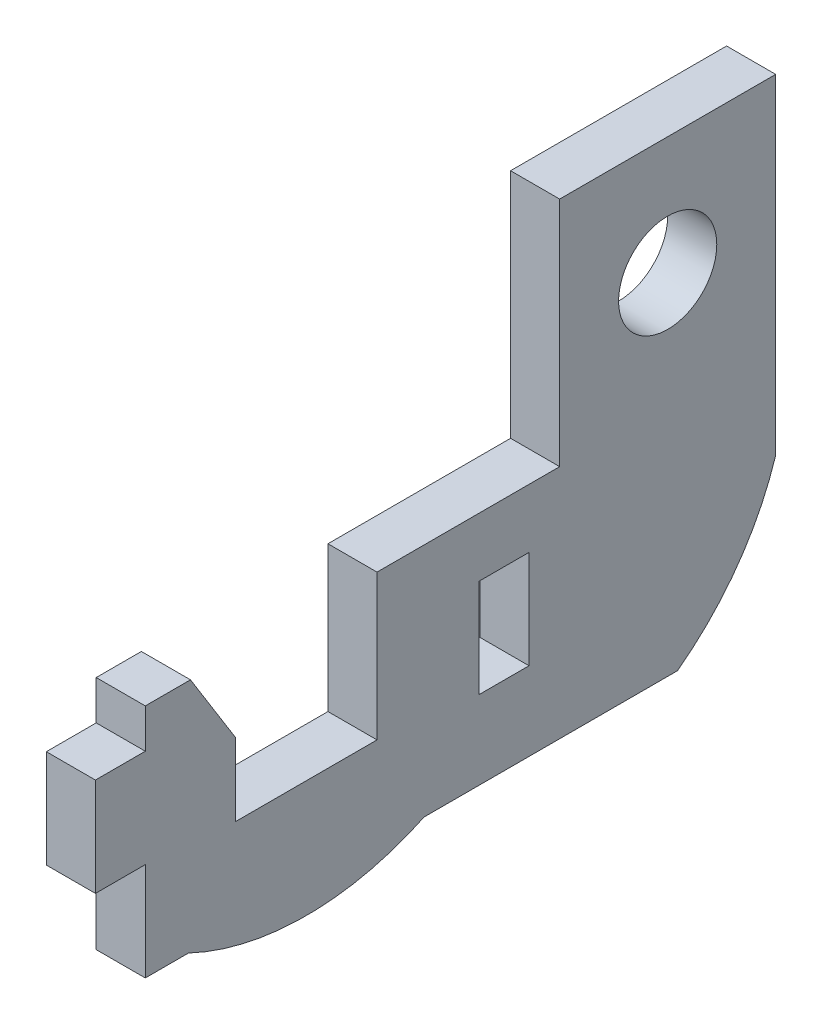
SolidWorks part; units mm, degrees
ref_plane "Front Plane" through (0, 0, 0) normal (0, 0, 1) x (1, 0, 0)
ref_plane "Top Plane" through (0, 0, 0) normal (0, 1, 0) x (1, 0, 0)
ref_plane "Right Plane" through (0, 0, 0) normal (1, 0, 0) x (0, 0, -1)
sketch "Sketch1" plane through (0, 0, 0) normal (1, 0, 0) x (0, 0, -1)
  line L0 (-6.985, 7.62) -> (6.985, 7.62)
  line L1 (-6.985, 7.62) -> (-6.985, -7.366)
  line L2 (-6.985, -7.366) -> (-18.796, -7.366)
  line L3 (-33.782, -7.366) -> (-33.782, -9.906)
  line L4 (-33.782, -9.906) -> (-37.0078, -9.906)
  line L5 (-37.0078, -9.906) -> (-37.0078, -16.256)
  line L6 (-37.0078, -16.256) -> (-33.782, -16.256)
  line L7 (-33.782, -16.256) -> (-33.782, -22.606)
  line L8 (-33.782, -22.606) -> (6.985, -22.606)
  line L9 (6.985, -22.606) -> (6.985, 7.62)
  line L10 (-37.0078, -13.081) -> (6.985, -13.081) construction
  line L11 (-18.796, -7.366) -> (-18.796, -16.764)
  line L13 (-8.9662, -11.176) -> (-12.192, -11.176)
  line L14 (-8.9662, -11.176) -> (-8.9662, -17.526)
  line L15 (-8.9662, -17.526) -> (-12.192, -17.526)
  line L16 (-12.192, -11.176) -> (-12.192, -17.526)
  line L17 (-8.9662, -11.176) -> (-12.192, -17.526) construction
  line L18 (-18.796, -16.764) -> (-27.94, -16.764)
  line L19 (-27.94, -16.764) -> (-27.94, -7.366)
  line L20 (-27.94, -7.366) -> (-33.782, -7.366)
  line L21 (-8.9662, -17.526) -> (-12.192, -11.176) construction
  circle A0 centre (0, 0) radius 3.175
  point P14 (-10.5791, -14.351)
  dimension "D11" = 3.2258
  dimension "D12" = 6.35
  dimension "D13" = 21.59
  dimension "D6" = 7.366
  dimension "D7" = 90
  dimension "D8" = 33.782
  dimension "D2" = 6.35
  dimension "D3" = 7.62
  dimension "D4" = 6.985
  dimension "D5" = 6.985
  dimension "D9" = 6.35
  dimension "D10" = 2.54
  dimension "D14" = 3.2258
  dimension "D15" = 6.35
  dimension "D16" = 5.842
  dimension "D17" = 9.144
  dimension "D18" = 9.398
  dimension "D19" = 5.08
extrude "Boss-Extrude1" add sketch "Sketch1" along normal blind 3.175
sketch "Sketch2" plane through (0, 0, 0) normal (-1, 0, 0) x (0, 0, 1)
  line L0 (23.368, -16.764) -> (23.368, -22.606) construction
  line L1 (18.796, -16.764) -> (27.94, -16.764) construction
  line L2 (33.782, -22.606) -> (-6.985, -22.606) construction
  line L4 (23.368, -22.606) -> (15.748, -22.606)
  line L5 (23.368, -22.606) -> (30.988, -22.606)
  arc A0 (15.748, -22.606) -> (30.988, -22.606) centre (23.368, -6.5416) ccw
  dimension "D1" = 7.62
  dimension "D3" = 17.78
  dimension "D2" = 7.62
extrude "add body at bottom" add sketch "Sketch2" against normal blind 3.175
sketch "Sketch3" plane through (0, 0, 0) normal (-1, 0, 0) x (0, 0, 1)
  line L0 (30.861, -7.366) -> (27.94, -12.065)
  line L1 (27.94, -7.366) -> (33.782, -7.366) construction
  line L2 (27.94, -16.764) -> (27.94, -7.366) construction
  line L3 (27.94, -12.065) -> (27.94, -7.366)
  line L4 (27.94, -7.366) -> (30.861, -7.366)
  line L5 (-6.985, -22.606) -> (-0.635, -22.606)
  line L6 (15.748, -22.606) -> (-6.985, -22.606) construction
  line L7 (-6.985, -22.606) -> (-6.985, -13.716)
  line L8 (-6.985, -22.606) -> (-6.985, 7.62) construction
  arc A0 (-6.985, -13.716) -> (-0.635, -22.606) centre (9.9585, -8.3264) ccw
  dimension "D1" = 2.921
  dimension "D2" = 4.699
  dimension "D3" = 6.35
  dimension "D4" = 8.89
extrude "Cut-Extrude1" cut sketch "Sketch3" against normal through all
